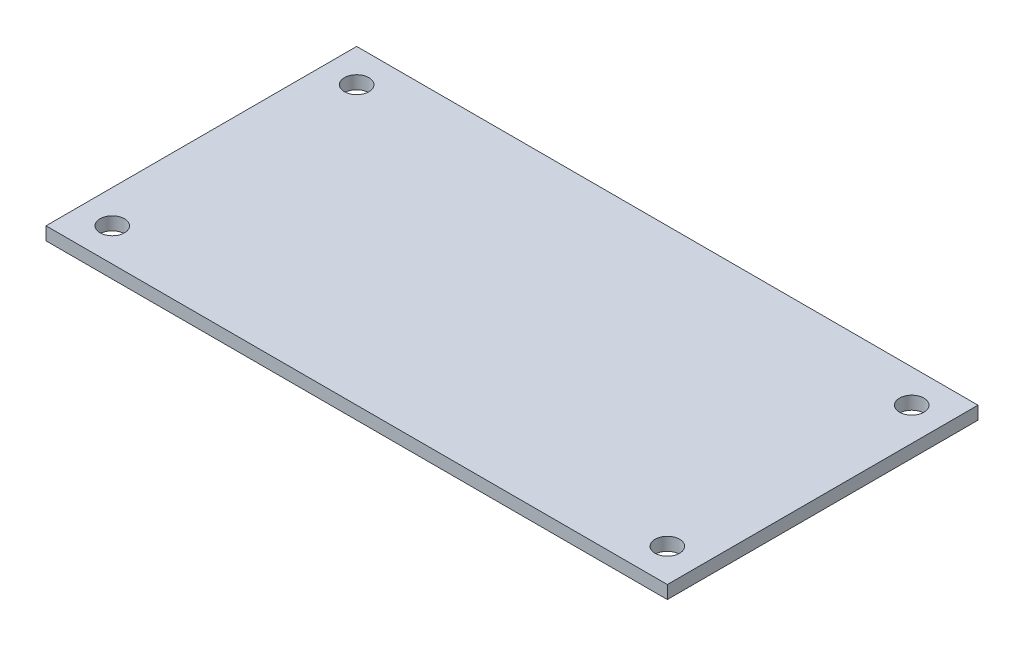
SolidWorks part; units mm, degrees
ref_plane "Front Plane" through (0, 0, 0) normal (0, 0, 1) x (1, 0, 0)
ref_plane "Top Plane" through (0, 0, 0) normal (0, 1, 0) x (1, 0, 0)
ref_plane "Right Plane" through (0, 0, 0) normal (1, 0, 0) x (0, 0, -1)
sketch "Sketch1" plane through (0, 0, 0) normal (0, 1, 0) x (1, 0, 0)
  line L0 (-34.036, 0) -> (34.036, 0) construction
  line L1 (38.1, -19.05) -> (-38.1, -19.05)
  line L2 (38.1, -19.05) -> (38.1, 19.05)
  line L3 (38.1, 19.05) -> (-38.1, 19.05)
  line L4 (-38.1, -19.05) -> (-38.1, 19.05)
  line L5 (38.1, -19.05) -> (-38.1, 19.05) construction
  line L6 (38.1, 19.05) -> (-38.1, -19.05) construction
  line L7 (-34.036, 14.986) -> (34.036, 14.986) construction
  line L8 (-34.036, 14.986) -> (-34.036, -14.986) construction
  line L9 (-34.036, -14.986) -> (34.036, -14.986) construction
  line L10 (34.036, 14.986) -> (34.036, -14.986) construction
  line L11 (0, 14.986) -> (0, -14.986) construction
  circle A0 centre (-34.036, 14.986) radius 1.5
  circle A1 centre (-34.036, -14.986) radius 1.5
  circle A2 centre (34.036, 14.986) radius 1.5
  circle A3 centre (34.036, -14.986) radius 1.5
  point P0 (0, 0)
  point P18 (0, 0)
  point P19 (0, 0)
  dimension "D3" = 3
  dimension "D1" = 76.2
  dimension "D2" = 38.1
  dimension "D4" = 29.972
  dimension "D5" = 68.072
extrude "Boss-Extrude1" add sketch "Sketch1" along normal blind 1.6
